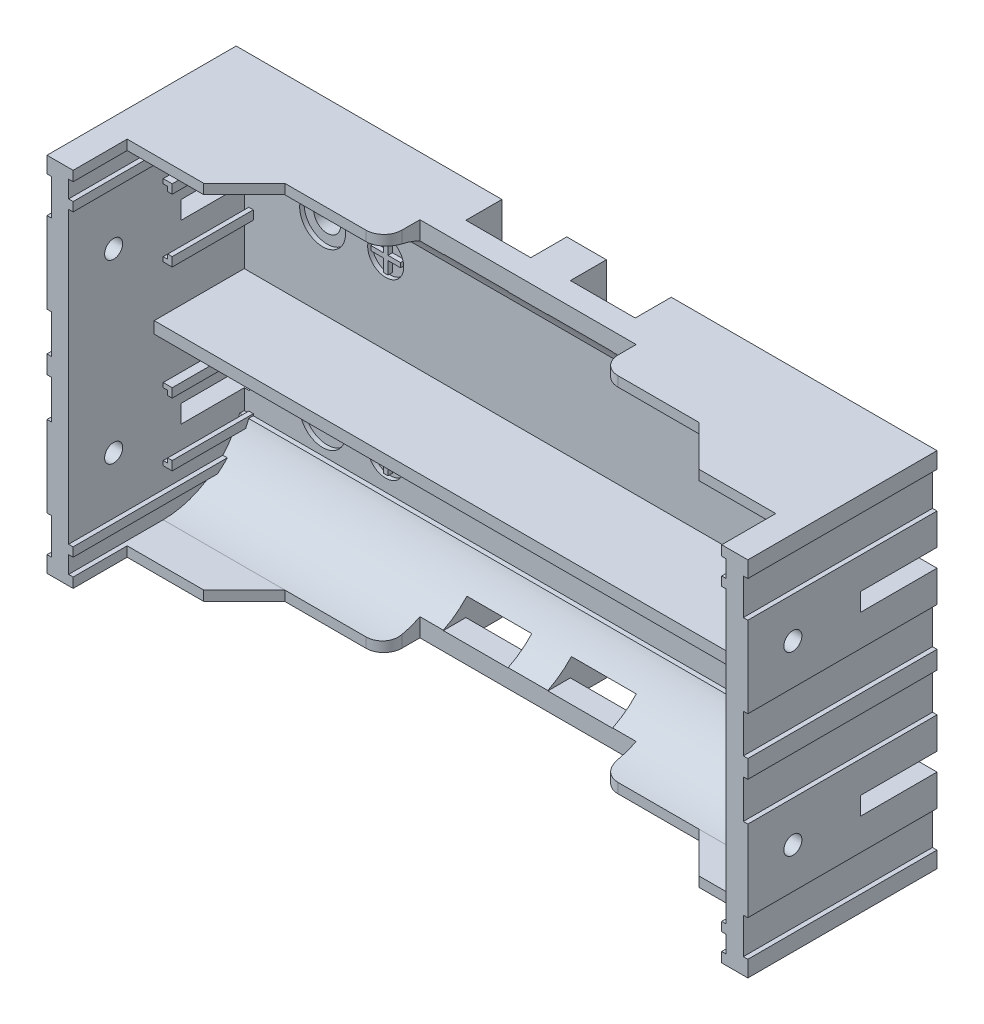
SolidWorks part; units mm, degrees
material "ABS"
ref_plane "Спереди" through (0, 0, 0) normal (0, 0, 1) x (1, 0, 0)
ref_plane "Сверху" through (0, 0, 0) normal (0, 1, 0) x (1, 0, 0)
ref_plane "Справа" through (0, 0, 0) normal (1, 0, 0) x (0, 0, -1)
sketch "Эскиз1" plane through (0, 0, 0) normal (0, 0, 1) x (1, 0, 0)
  line L0 (-38.9, 20.1) -> (38.9, 20.1)
  line L1 (38.9, 20.1) -> (38.9, 18.3)
  line L2 (38.9, -20.1) -> (-38.9, -20.1)
  line L3 (38.9, 18.3) -> (38.4, 18.3)
  line L4 (38.4, 18.3) -> (38.4, 14.3)
  line L5 (38.4, 14.3) -> (38.9, 14.3)
  line L6 (38.9, 14.3) -> (38.9, 5.3)
  line L7 (38.9, 5.3) -> (38.4, 5.3)
  line L8 (38.4, 5.3) -> (38.4, 1)
  line L9 (38.4, 1) -> (38.9, 1)
  line L10 (38.9, 1) -> (38.9, -1)
  line L11 (38.9, -1) -> (38.4, -1)
  line L12 (38.4, -1) -> (38.4, -5.3)
  line L13 (38.4, -5.3) -> (38.9, -5.3)
  line L14 (38.9, -5.3) -> (38.9, -14.3)
  line L15 (38.9, -14.3) -> (38.4, -14.3)
  line L16 (38.4, -14.3) -> (38.4, -18.3)
  line L17 (38.4, -18.3) -> (38.9, -18.3)
  line L18 (38.9, -18.3) -> (38.9, -20.1)
  line L19 (-38.9, 20.1) -> (-38.9, 18.3)
  line L20 (-38.9, 18.3) -> (-38.4, 18.3)
  line L21 (-38.4, 18.3) -> (-38.4, 14.3)
  line L22 (-38.4, 14.3) -> (-38.9, 14.3)
  line L23 (-38.9, 14.3) -> (-38.9, 5.3)
  line L24 (-38.9, 5.3) -> (-38.4, 5.3)
  line L25 (-38.4, 5.3) -> (-38.4, 1)
  line L26 (-38.4, 1) -> (-38.9, 1)
  line L27 (-38.9, 1) -> (-38.9, -1)
  line L28 (-38.9, -1) -> (-38.4, -1)
  line L29 (-38.4, -1) -> (-38.4, -5.3)
  line L30 (-38.4, -5.3) -> (-38.9, -5.3)
  line L31 (-38.9, -5.3) -> (-38.9, -14.3)
  line L32 (-38.9, -14.3) -> (-38.4, -14.3)
  line L33 (-38.4, -14.3) -> (-38.4, -18.3)
  line L34 (-38.4, -18.3) -> (-38.9, -18.3)
  line L35 (-38.9, -18.3) -> (-38.9, -20.1)
  circle A0 centre (27.8, 9.65) radius 1.6
  circle A1 centre (-27.8, 9.65) radius 1.5
  circle A2 centre (-27.8, -9.65) radius 1.5
  circle A3 centre (27.8, -9.65) radius 1.5
extrude "Основание" add sketch "Эскиз1" along normal blind 1.5
sketch "Эскиз2" plane through (0, 0, 1.5) normal (0, 0, 1) x (1, 0, 0)
  line L0 (38.9, 20.1) -> (36.5, 20.1)
  line L1 (38.9, 20.1) -> (-38.9, 20.1) construction
  line L2 (-38.9, 20.1) -> (-36.5, 20.1)
  line L3 (38.9, 20.1) -> (38.9, 18.3)
  line L4 (38.9, 18.3) -> (38.4, 18.3)
  line L5 (38.4, 18.3) -> (38.4, 14.3)
  line L6 (38.4, 14.3) -> (38.9, 14.3)
  line L7 (38.9, 14.3) -> (38.9, 5.3)
  line L8 (38.9, 5.3) -> (38.4, 5.3)
  line L9 (38.4, 5.3) -> (38.4, 1)
  line L10 (38.4, 1) -> (38.9, 1)
  line L11 (38.9, 1) -> (38.9, -1)
  line L12 (38.9, -1) -> (38.4, -1)
  line L13 (38.4, -1) -> (38.4, -5.3)
  line L14 (38.4, -5.3) -> (38.9, -5.3)
  line L15 (38.9, -5.3) -> (38.9, -14.3)
  line L16 (38.9, -14.3) -> (38.4, -14.3)
  line L17 (38.4, -14.3) -> (38.4, -18.3)
  line L18 (38.4, -18.3) -> (38.9, -18.3)
  line L19 (38.9, -18.3) -> (38.9, -20.1)
  line L20 (38.9, -20.1) -> (36.5, -20.1)
  line L21 (-38.9, -20.1) -> (38.9, -20.1) construction
  line L22 (36.5, -20.1) -> (36.5, 20.1)
  line L23 (-38.9, 20.1) -> (-38.9, 18.3)
  line L24 (-38.9, 18.3) -> (-38.4, 18.3)
  line L25 (-38.4, 18.3) -> (-38.4, 14.3)
  line L26 (-38.4, 14.3) -> (-38.9, 14.3)
  line L27 (-38.9, 14.3) -> (-38.9, 5.3)
  line L28 (-38.9, 5.3) -> (-38.4, 5.3)
  line L29 (-38.4, 5.3) -> (-38.4, 1)
  line L30 (-38.4, 1) -> (-38.9, 1)
  line L31 (-38.9, 1) -> (-38.9, -1)
  line L32 (-38.9, -1) -> (-38.4, -1)
  line L33 (-38.4, -1) -> (-38.4, -5.3)
  line L34 (-38.4, -5.3) -> (-38.9, -5.3)
  line L35 (-38.9, -5.3) -> (-38.9, -14.3)
  line L36 (-38.9, -14.3) -> (-38.4, -14.3)
  line L37 (-38.4, -14.3) -> (-38.4, -18.3)
  line L38 (-38.4, -18.3) -> (-38.9, -18.3)
  line L39 (-38.9, -18.3) -> (-38.9, -20.1)
  line L40 (-38.9, -20.1) -> (-36.5, -20.1)
  line L41 (-36.5, -20.1) -> (-36.5, 20.1)
extrude "Борта малые" add sketch "Эскиз2" along normal blind 19.5
sketch "Эскиз5" plane through (0, 0, 1.5) normal (0, 0, 1) x (1, 0, 0)
  line L0 (-37, 20.1) -> (37, 20.1)
  line L1 (-36.5, 20.1) -> (-38.9, 20.1) construction
  line L2 (38.9, 20.1) -> (36.5, 20.1) construction
  line L3 (37, 20.1) -> (37, 19)
  line L4 (37, 19) -> (-37, 19)
  line L5 (-37, 19) -> (-37, 20.1)
  line L6 (-37, -20.1) -> (-37, -19)
  line L7 (-38.9, -20.1) -> (-36.5, -20.1) construction
  line L8 (37, -20.1) -> (37, -19)
  line L9 (36.5, -20.1) -> (38.9, -20.1) construction
  line L10 (37, -19) -> (-37, -19)
  line L11 (-37, -20.1) -> (37, -20.1)
extrude "Борта большие" add sketch "Эскиз5" along normal blind 13.5
sketch "Эскиз7" plane through (-36.5, 0, 0) normal (1, 0, 0) x (0, 0, -1)
  line L0 (-1.5, 19) -> (-10.5, 19)
  line L1 (-1.5, 19) -> (-1.5, 13)
  line L2 (-1.5, 13) -> (-2.0147, 13)
  line L4 (-1.5, -19) -> (-1.5, -13)
  line L5 (-1.5, -19) -> (-1.5, 19) construction
  line L6 (-1.5, -19) -> (-10.5, -19)
  line L7 (-1.5, -19) -> (-15, -19) construction
  line L9 (-1.5, -13) -> (-2.0147, -13)
  arc A2 (-10.5, 19) -> (-2.0147, 13) centre (-10.5, 10) cw
  arc A4 (-10.5, -19) -> (-2.0147, -13) centre (-10.5, -10) ccw
extrude "Бобышка-Вытянуть5" add sketch "Эскиз7" along normal blind 74
sketch "Эскиз6" plane through (0, -20.1, 0) normal (0, -1, 0) x (1, 0, 0)
  line L0 (-36.5, 15) -> (-27.5, 15)
  line L1 (-36.5, 15) -> (36.5, 15) construction
  line L5 (36.5, 15) -> (27.5, 15)
  line L8 (-27.5, 15) -> (-23, 10.5)
  line L9 (-23, 10.5) -> (-14, 10.5)
  line L10 (27.5, 15) -> (23, 10.5)
  line L11 (12, 8.5) -> (12, 6.5)
  line L12 (-12, 8.5) -> (-12, 6.5)
  line L13 (14, 10.5) -> (23, 10.5)
  line L14 (12, 6.5) -> (-12, 6.5)
  line L15 (-36.5, 15) -> (-36.5, 21)
  line L16 (-36.5, 21) -> (36.5, 21)
  line L17 (36.5, 21) -> (36.5, 15)
  arc A0 (-14, 10.5) -> (-12, 8.5) centre (-14, 8.5) cw
  arc A1 (14, 10.5) -> (12, 8.5) centre (14, 8.5) ccw
extrude "Борта большие обрез" cut sketch "Эскиз6" against normal blind 45
sketch "Эскиз3" plane through (0, 0, 1.5) normal (0, 0, 1) x (1, 0, 0)
  line L0 (-20.55, 11.3) -> (-20.55, 9.9)
  line L1 (-20.55, 9.9) -> (-19.15, 9.9)
  line L2 (-21.05, 9.9) -> (-21.05, 11.3)
  line L3 (-21.05, 11.3) -> (-20.55, 11.3)
  line L4 (-19.15, 9.9) -> (-19.15, 9.4)
  line L5 (-19.15, 9.4) -> (-20.55, 9.4)
  line L6 (-20.55, 9.4) -> (-20.55, 8)
  line L7 (-20.55, 8) -> (-21.05, 8)
  line L8 (-21.05, 8) -> (-21.05, 9.4)
  line L9 (-21.05, 9.4) -> (-22.45, 9.4)
  line L10 (-22.45, 9.4) -> (-22.45, 9.9)
  line L11 (-22.45, 9.9) -> (-21.05, 9.9)
  line L12 (-21.05, -8) -> (-20.55, -8)
  line L13 (-20.55, -8) -> (-20.55, -9.4)
  line L14 (-21.05, -9.4) -> (-21.05, -8)
  line L15 (-20.55, -9.4) -> (-19.15, -9.4)
  line L16 (-19.15, -9.4) -> (-19.15, -9.9)
  line L17 (-19.15, -9.9) -> (-20.55, -9.9)
  line L18 (-20.55, -9.9) -> (-20.55, -11.3)
  line L19 (-20.55, -11.3) -> (-21.05, -11.3)
  line L20 (-21.05, -11.3) -> (-21.05, -9.9)
  line L21 (-21.05, -9.9) -> (-22.45, -9.9)
  line L22 (-22.45, -9.9) -> (-22.45, -9.4)
  line L23 (-22.45, -9.4) -> (-21.05, -9.4)
  line L25 (20.8, 9.9) -> (19.15, 9.9)
  line L26 (20.8, 9.9) -> (22.45, 9.9)
  line L27 (19.15, 9.9) -> (19.15, 9.4)
  line L28 (19.15, 9.4) -> (22.45, 9.4)
  line L29 (22.45, 9.4) -> (22.45, 9.9)
  line L30 (20.8, -9.4) -> (19.15, -9.4)
  line L31 (19.15, -9.4) -> (19.15, -9.9)
  line L32 (19.15, -9.9) -> (22.45, -9.9)
  line L33 (22.45, -9.9) -> (22.45, -9.4)
  line L34 (22.45, -9.4) -> (20.8, -9.4)
  circle A0 centre (-27.8, 9.65) radius 2.55
  circle A1 centre (27.8, 9.65) radius 2.55
  circle A2 centre (-27.8, -9.65) radius 2.55
  circle A3 centre (27.8, -9.65) radius 2.55
  circle A4 centre (-20.8, 9.65) radius 2
  circle A5 centre (-20.8, -9.65) radius 2
  circle A6 centre (20.8, 9.65) radius 2
  circle A7 centre (20.8, -9.65) radius 2
extrude "Вырез-Вытянуть1" cut sketch "Эскиз3" against normal blind 0.5
sketch "Эскиз4" plane through (0, 0, 1.5) normal (0, 0, 1) x (1, 0, 0)
  line L0 (-37, 0) -> (-37, 0.65)
  line L1 (-37, 0.65) -> (37, 0.65)
  line L2 (37, 0.65) -> (37, -0.65)
  line L3 (37, -0.65) -> (-37, -0.65)
  line L4 (-37, -0.65) -> (-37, 0)
extrude "Борт центральный" add sketch "Эскиз4" along normal blind 10
sketch "Эскиз8" plane through (0, 0, 1.5) normal (0, 0, 1) x (1, 0, 0)
  line L0 (-36.5, 20.1) -> (-36, 20.1)
  line L1 (-27.5, 20.1) -> (-36.5, 20.1) construction
  line L2 (-36, 20.1) -> (-36, 19)
  line L3 (-36.5, 19) -> (-27.5, 19) construction
  line L4 (-36, 19) -> (-36.5, 19)
  line L5 (-36.5, 19) -> (-36.5, 20.1)
  line L6 (-36.5, -20.1) -> (-36.5, -19)
  line L7 (-36.5, 13) -> (-36.5, 19) construction
  line L8 (-36.5, 17.1) -> (-36, 17.1)
  line L9 (-36, 17.1) -> (-36, 16.1)
  line L10 (-36, 16.1) -> (-36.5, 16.1)
  line L11 (-36.5, -20.1) -> (-36.5, 20.1) construction
  line L12 (-36.5, 16.1) -> (-36.5, 17.1)
  line L13 (-36.5, -19) -> (-36, -19)
  line L14 (-23, -19) -> (-36.5, -19) construction
  line L15 (-36, -19) -> (-36, -20.1)
  line L16 (-36.5, -20.1) -> (-27.5, -20.1) construction
  line L17 (-36, -20.1) -> (-36.5, -20.1)
  line L18 (36.5, -20.1) -> (36.5, -19)
  line L19 (-36.5, -17.1) -> (-36, -17.1)
  line L20 (-36, -17.1) -> (-36, -16.1)
  line L21 (-36, -16.1) -> (-36.5, -16.1)
  line L22 (-36.5, -16.1) -> (-36.5, -17.1)
  line L23 (36.5, 20.1) -> (36.5, -20.1) construction
  line L24 (36.5, -19) -> (36.5, -20.1) construction
  line L25 (36.5, -19) -> (36, -19)
  line L26 (36.5, -19) -> (23, -19) construction
  line L27 (36, -19) -> (36, -20.1)
  line L28 (27.5, -20.1) -> (36.5, -20.1) construction
  line L29 (36, -20.1) -> (36.5, -20.1)
  line L30 (36.5, -17.1) -> (36, -17.1)
  line L31 (36, -17.1) -> (36, -16.1)
  line L32 (36, -16.1) -> (36.5, -16.1)
  line L33 (36.5, -16.1) -> (36.5, -17.1)
  line L34 (36.5, 20.1) -> (36.5, 19)
  line L35 (36.5, 19) -> (36, 19)
  line L36 (-36.5, 19) -> (36.5, 19) construction
  line L37 (36, 19) -> (36, 20.1)
  line L38 (36.5, 20.1) -> (27.5, 20.1) construction
  line L39 (36, 20.1) -> (36.5, 20.1)
  line L40 (36.5, 17.1) -> (36, 17.1)
  line L41 (36, 17.1) -> (36, 16.1)
  line L42 (36, 16.1) -> (36.5, 16.1)
  line L43 (36.5, 19) -> (36.5, 13) construction
  line L44 (36.5, 16.1) -> (36.5, 17.1)
extrude "Бобышка-Вытянуть6" add sketch "Эскиз8" along normal blind 19.5
sketch "Эскиз9" plane through (38.9, 0, 0) normal (1, 0, 0) x (0, 0, -1)
  line L0 (0, 9.8) -> (0, 10.8)
  line L1 (0, 5.3) -> (0, 14.3) construction
  line L2 (0, 10.8) -> (-8.5, 10.8)
  line L3 (-8.5, 10.8) -> (-8.5, 8.8)
  line L4 (-8.5, 8.8) -> (0, 8.8)
  line L5 (0, 8.8) -> (0, 9.8)
  line L6 (0, -9.8) -> (0, -8.8)
  line L7 (0, -14.3) -> (0, -5.3) construction
  line L8 (0, -8.8) -> (-8.5, -8.8)
  line L9 (-8.5, -8.8) -> (-8.5, -10.8)
  line L10 (-8.5, -10.8) -> (0, -10.8)
  line L11 (0, -10.8) -> (0, -9.8)
  line L12 (-21, 9.8) -> (-16, 9.8) construction
  line L13 (-21, 5.3) -> (-21, 14.3) construction
  circle A0 centre (-16, 9.8) radius 1
  circle A1 centre (-16, -9.8) radius 1
extrude "Вырез-Вытянуть3" cut sketch "Эскиз9" against normal blind 3
sketch "Эскиз10" plane through (-38.9, 0, 0) normal (-1, 0, 0) x (0, 0, 1)
  line L0 (0, 9.8) -> (0, 10.8)
  line L1 (0, 14.3) -> (0, 5.3) construction
  line L2 (0, 10.8) -> (8.5, 10.8)
  line L3 (8.5, 10.8) -> (8.5, 8.8)
  line L4 (8.5, 8.8) -> (0, 8.8)
  line L5 (0, 8.8) -> (0, 9.8)
  line L6 (0, -9.8) -> (0, -8.8)
  line L8 (0, -5.3) -> (0, -14.3) construction
  line L9 (0, -8.8) -> (8.5, -8.8)
  line L10 (8.5, -8.8) -> (8.5, -10.8)
  line L11 (8.5, -10.8) -> (0, -10.8)
  line L12 (0, -10.8) -> (0, -9.8)
  line L13 (16, 9.8) -> (21, 9.8) construction
  line L14 (21, 14.3) -> (21, 5.3) construction
  circle A0 centre (16, 9.8) radius 1
  circle A1 centre (16, -9.8) radius 1
extrude "Вырез-Вытянуть4" cut sketch "Эскиз10" against normal blind 3
sketch "Эскиз11" plane through (0, 0, 1.5) normal (0, 0, 1) x (1, 0, 0)
  line L0 (-35.9, 9.8) -> (-36.5, 9.8) construction
  line L1 (-35.9, 8.8) -> (-35.9, 10.8) construction
  line L2 (-36.5, -16.1) -> (-36.5, 16.1) construction
  line L3 (-36, 12.8) -> (-35.5, 12.8)
  line L4 (-36.5, 13) -> (-36.5, 16.1) construction
  line L5 (-36.5, 13.3) -> (-36, 13.3)
  line L6 (-36, 13.3) -> (-36, 12.8)
  line L7 (-35.5, 12.8) -> (-35.5, 13.8)
  line L8 (-35.5, 13.8) -> (-36.5, 13.8)
  line L9 (-36.5, 13.8) -> (-36.5, 13.3)
  line L10 (-36.5, 9.8) -> (-36.5, 6.3) construction
  line L11 (-36.5, 0.65) -> (-36.5, 8.8) construction
  line L12 (-36.5, 6.3) -> (-36, 6.3)
  line L13 (-36, 6.3) -> (-36, 6.8)
  line L14 (-36, 6.8) -> (-35.5, 6.8)
  line L15 (-35.5, 6.8) -> (-35.5, 5.8)
  line L16 (-35.5, 5.8) -> (-36.5, 5.8)
  line L17 (-36.5, 5.8) -> (-36.5, 6.3)
  line L18 (-36.5, -9.8) -> (-36.5, -6.3) construction
  line L19 (-36.5, -6.3) -> (-36, -6.3)
  line L20 (-36, -6.3) -> (-36, -6.8)
  line L21 (-36, -6.8) -> (-35.5, -6.8)
  line L22 (-35.5, -6.8) -> (-35.5, -5.8)
  line L23 (-35.5, -5.8) -> (-36.5, -5.8)
  line L24 (-36.5, -8.8) -> (-36.5, -0.65) construction
  line L25 (-36.5, -5.8) -> (-36.5, -6.3)
  line L26 (-36.5, -13.3) -> (-36, -13.3)
  line L28 (-36.5, -9.8) -> (-36.5, -13.3) construction
  line L29 (-36.5, -13) -> (-36.5, -10.8) construction
  line L30 (-36, -13.3) -> (-36, -12.8)
  line L31 (-36, -12.8) -> (-35.5, -12.8)
  line L33 (-35.5, -13.8) -> (-36.5, -13.8)
  line L34 (-36.5, -16.1) -> (-36.5, -13) construction
  line L35 (-36.5, -13.8) -> (-36.5, -13.3)
  line L36 (35.5, 13.8) -> (35.5, 12.8)
  line L37 (36.5, 16.1) -> (36.5, -16.1) construction
  line L38 (36.5, 13.8) -> (35.5, 13.8)
  line L39 (35.5, 12.8) -> (36, 12.8)
  line L40 (36, 12.8) -> (36, 13.3)
  line L41 (36, 13.3) -> (36.5, 13.3)
  line L42 (36.5, 16.1) -> (36.5, 13) construction
  line L43 (36.5, 13.3) -> (36.5, 13.8)
  line L44 (36.5, 5.8) -> (35.5, 5.8)
  line L45 (36.5, 8.8) -> (36.5, 0.65) construction
  line L46 (35.5, 5.8) -> (35.5, 6.8)
  line L47 (35.5, 6.8) -> (36, 6.8)
  line L48 (36, 6.8) -> (36, 6.3)
  line L49 (36, 6.3) -> (36.5, 6.3)
  line L50 (36.5, 6.3) -> (36.5, 5.8)
  line L51 (35.5, -5.8) -> (36.5, -5.8)
  line L52 (36.5, -0.65) -> (36.5, -8.8) construction
  line L53 (35.5, -5.8) -> (35.5, -6.8)
  line L54 (35.5, -6.8) -> (36, -6.8)
  line L55 (36, -6.8) -> (36, -6.3)
  line L56 (36, -6.3) -> (36.5, -6.3)
  line L57 (36.5, -6.3) -> (36.5, -5.8)
  line L58 (36.5, -13.3) -> (36.5, -13.8)
  line L59 (36.5, -13) -> (36.5, -16.1) construction
  line L60 (36.5, -13.8) -> (35.5, -13.8)
  line L61 (35.5, -13.8) -> (35.5, -12.8)
  line L62 (35.5, -12.8) -> (36, -12.8)
  line L63 (36, -12.8) -> (36, -13.3)
  line L64 (36, -13.3) -> (36.5, -13.3)
  line L65 (-35.5, -13.8) -> (-35.5, -12.8)
extrude "Держатель контакта" add sketch "Эскиз11" along normal blind 9
sketch "Эскиз12" plane through (0, 0, 0) normal (0, 0, -1) x (-1, 0, 0)
  line L0 (-38.9, 20.1) -> (-9.4, 20.1) construction
  line L1 (-38.9, 20.1) -> (38.9, 20.1) construction
  line L2 (-9.4, 20.1) -> (-9.4, 16.1)
  line L3 (-9.4, 16.1) -> (-2.2, 16.1)
  line L4 (-2.2, 16.1) -> (-2.2, 20.1)
  line L5 (-2.2, 20.1) -> (-9.4, 20.1)
  line L6 (38.9, 20.1) -> (9.4, 20.1) construction
  line L7 (9.4, 20.1) -> (9.4, 16.1)
  line L8 (9.4, 16.1) -> (2.2, 16.1)
  line L9 (2.2, 16.1) -> (2.2, 20.1)
  line L10 (2.2, 20.1) -> (9.4, 20.1)
  line L11 (-9.4, -20.1) -> (-9.4, -16.1)
  line L12 (38.9, -20.1) -> (-38.9, -20.1) construction
  line L13 (-9.4, -16.1) -> (-2.2, -16.1)
  line L14 (-2.2, -16.1) -> (-2.2, -20.1)
  line L15 (-2.2, -20.1) -> (-9.4, -20.1)
  line L16 (2.2, -16.1) -> (2.2, -20.1)
  line L17 (2.2, -20.1) -> (9.4, -20.1)
  line L18 (9.4, -20.1) -> (9.4, -16.1)
  line L19 (9.4, -16.1) -> (2.2, -16.1)
extrude "Вырез-Вытянуть5" cut sketch "Эскиз12" against normal blind 4
sketch "Эскиз13" plane through (0, 0, 4) normal (0, 0, -1) x (-1, 0, 0)
  line L0 (-9.4, 20.1) -> (-9.4, 18.1) construction
  line L1 (-9.4, 20.1) -> (-9.4, 16.1) construction
  line L2 (-9.4, 18.1) -> (-2.2, 18.1)
  line L3 (-2.2, 16.1) -> (-2.2, 20.1) construction
  line L4 (-2.2, 18.1) -> (-2.2, 16.1)
  line L5 (-2.2, 16.1) -> (-9.4, 16.1)
  line L6 (-9.4, 16.1) -> (-9.4, 18.1)
  line L7 (2.2, 18.1) -> (9.4, 18.1)
  line L8 (2.2, 20.1) -> (2.2, 16.1) construction
  line L9 (9.4, 16.1) -> (9.4, 20.1) construction
  line L10 (9.4, 18.1) -> (9.4, 16.1)
  line L11 (9.4, 16.1) -> (2.2, 16.1)
  line L12 (2.2, 16.1) -> (2.2, 18.1)
  line L15 (-9.4, -16.1) -> (-2.2, -16.1)
  line L19 (-9.4, -16.1) -> (-9.4, -18.1)
  line L20 (-9.4, -16.1) -> (-9.4, -20.1) construction
  line L21 (-9.4, -18.1) -> (-2.2, -18.1)
  line L22 (-2.2, -20.1) -> (-2.2, -16.1) construction
  line L23 (-2.2, -18.1) -> (-2.2, -16.1)
  line L24 (2.2, -16.1) -> (2.2, -18.1)
  line L25 (2.2, -16.1) -> (2.2, -20.1) construction
  line L26 (2.2, -18.1) -> (9.4, -18.1)
  line L27 (9.4, -20.1) -> (9.4, -16.1) construction
  line L28 (9.4, -18.1) -> (9.4, -16.1)
  line L29 (9.4, -16.1) -> (2.2, -16.1)
extrude "Вырез-Вытянуть6" cut sketch "Эскиз13" against normal blind 4
sketch "Эскиз14" plane through (0, 0, 0) normal (0, 0, -1) x (-1, 0, 0)
  circle A0 centre (-27.8, 9.65) radius 2.9
  circle A1 centre (-27.8, -9.65) radius 2.9
  circle A2 centre (27.8, 9.65) radius 2.9
  circle A3 centre (27.8, -9.65) radius 2.9
  circle A4 centre (-27.8, 9.65) radius 1.5
  circle A5 centre (-27.8, -9.65) radius 1.5
  circle A6 centre (27.8, 9.65) radius 1.5
  circle A7 centre (27.8, -9.65) radius 1.5
extrude "Бобышка-Вытянуть7" add sketch "Эскиз14" along normal blind 0.4
